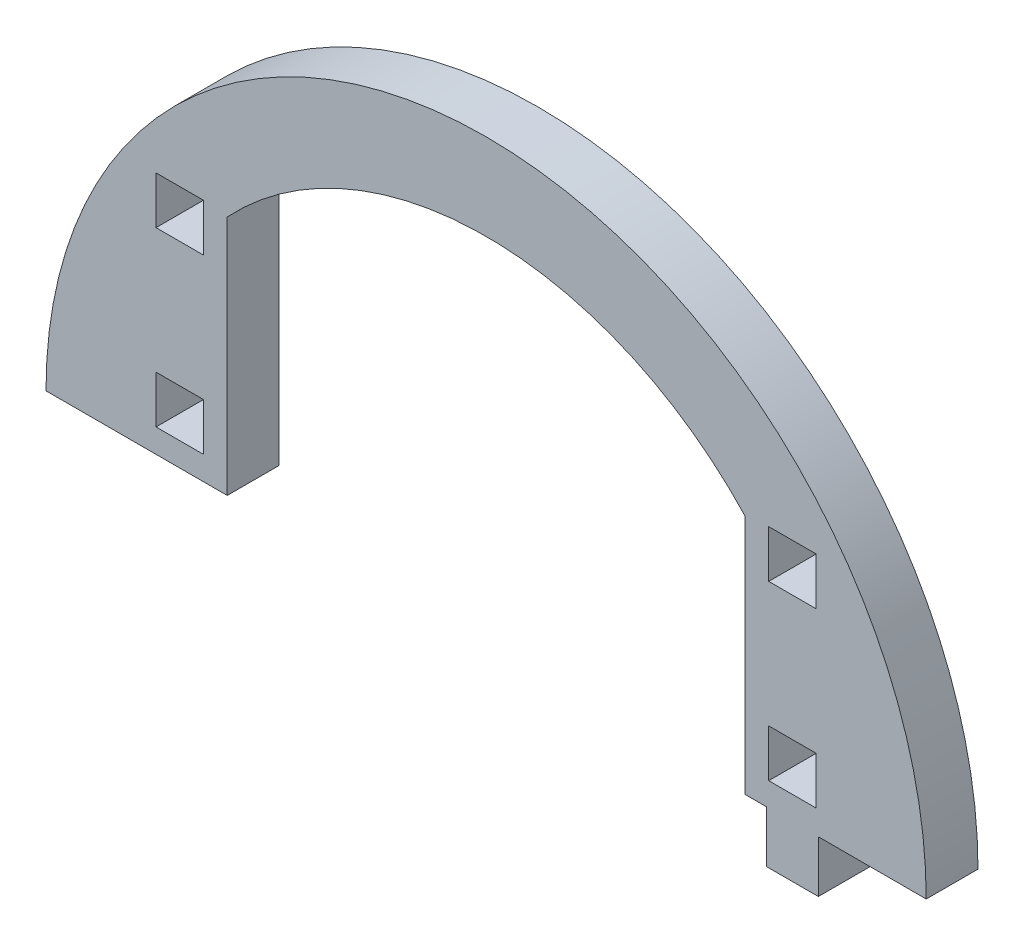
SolidWorks part; units mm, degrees
ref_plane "Front Plane" through (0, 0, 0) normal (0, 0, 1) x (1, 0, 0)
ref_plane "Top Plane" through (0, 0, 0) normal (0, 1, 0) x (1, 0, 0)
ref_plane "Right Plane" through (0, 0, 0) normal (1, 0, 0) x (0, 0, -1)
sketch "Model" plane through (0, 0, 0) normal (0, 0, 1) x (1, 0, 0)
  line L0 (3385.4376, 1476.8403) -> (3395.4376, 1476.8403)
  line L1 (3474.6876, 1485.0903) -> (3469.1876, 1485.0903)
  line L2 (3469.1876, 1485.0903) -> (3469.1876, 1479.5903)
  line L3 (3469.1876, 1479.5903) -> (3474.6876, 1479.5903)
  line L4 (3474.6876, 1479.5903) -> (3474.6876, 1485.0903)
  line L5 (3466.4376, 1476.8403) -> (3468.9376, 1476.8403)
  line L6 (3468.9376, 1476.8403) -> (3468.9376, 1470.8403)
  line L7 (3468.9376, 1470.8403) -> (3474.9376, 1470.8403)
  line L8 (3474.9376, 1470.8403) -> (3474.9376, 1476.8403)
  line L9 (3474.6876, 1505.0903) -> (3469.1876, 1505.0903)
  line L10 (3469.1876, 1505.0903) -> (3469.1876, 1499.5903)
  line L11 (3469.1876, 1499.5903) -> (3474.6876, 1499.5903)
  line L12 (3474.6876, 1499.5903) -> (3474.6876, 1505.0903)
  line L13 (3403.6876, 1485.0903) -> (3398.1876, 1485.0903)
  line L14 (3398.1876, 1485.0903) -> (3398.1876, 1479.5903)
  line L15 (3398.1876, 1479.5903) -> (3403.6876, 1479.5903)
  line L16 (3403.6876, 1479.5903) -> (3403.6876, 1485.0903)
  line L17 (3395.4376, 1476.8403) -> (3406.4376, 1476.8403)
  line L18 (3403.6876, 1505.0903) -> (3398.1876, 1505.0903)
  line L19 (3398.1876, 1505.0903) -> (3398.1876, 1499.5903)
  line L20 (3398.1876, 1499.5903) -> (3403.6876, 1499.5903)
  line L21 (3403.6876, 1499.5903) -> (3403.6876, 1505.0903)
  line L22 (3406.4376, 1504.7866) -> (3406.4376, 1476.8403)
  line L23 (3466.4376, 1504.7866) -> (3466.4376, 1476.8403)
  line L24 (3474.9376, 1476.8403) -> (3487.4376, 1476.8403)
  arc A0 (3487.4376, 1476.8403) -> (3385.4376, 1476.8403) centre (3436.4376, 1476.8403) ccw
  arc A1 (3466.4376, 1504.7866) -> (3406.4376, 1504.7866) centre (3436.4376, 1476.8403) ccw
extrude "Boss-Extrude1" add sketch "Model" along normal blind 6 contours L20 L21 L18 L19 | L11 L12 L9 L10 | L3 L4 L1 L2 | A0 L0 L17 L22 A1 L23 L5 L6 L7 L8 L24 | L13 L14 L15 L16
